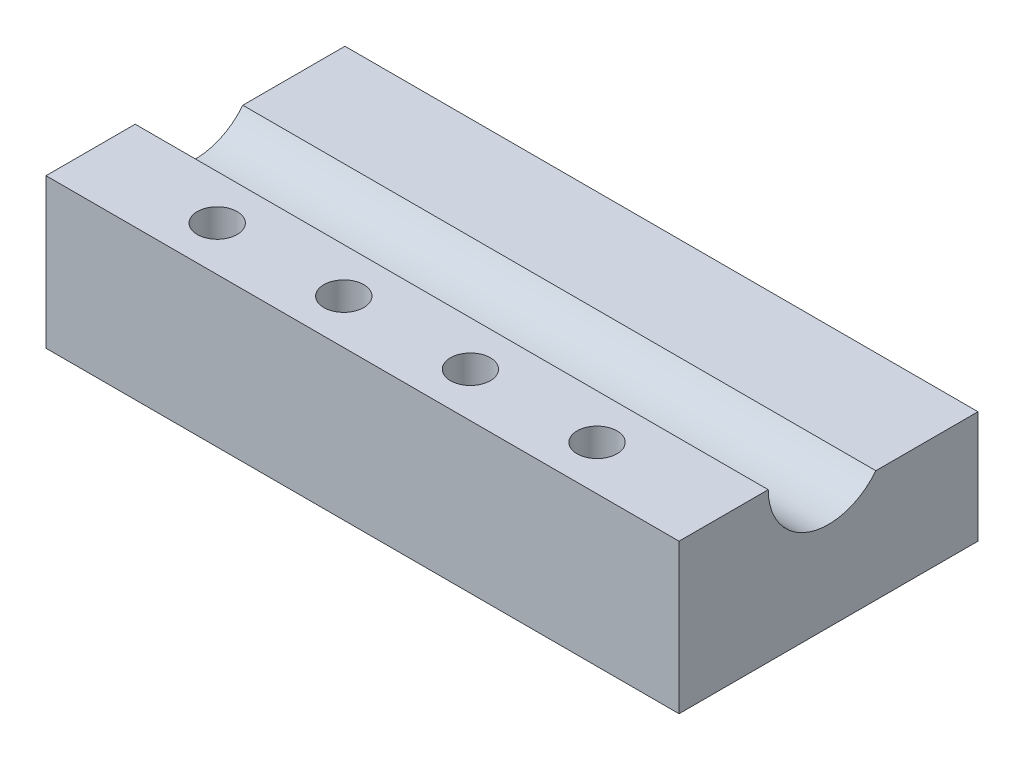
SolidWorks part; units mm, degrees
ref_plane "Front Plane" through (0, 0, 0) normal (0, 0, 1) x (1, 0, 0)
ref_plane "Top Plane" through (0, 0, 0) normal (0, 1, 0) x (1, 0, 0)
ref_plane "Right Plane" through (0, 0, 0) normal (1, 0, 0) x (0, 0, -1)
sketch "Sketch1" plane through (0, 0, 0) normal (0, 1, 0) x (1, 0, 0)
  line L1 (0, 0) -> (25.41, 0)
  line L2 (0, 0) -> (0, 12)
  line L3 (0, 12) -> (25.41, 12)
  line L4 (25.41, 0) -> (25.41, 12)
extrude "Boss-Extrude1" add sketch "Sketch1" along normal blind 6 contours L2 L3 L4 L1
sketch "Sketch2" plane through (0, 0, 0) normal (-1, 0, 0) x (0, 0, 1)
  line L0 (0, 6) -> (-12, 6) construction
  circle A0 centre (-6, 6) radius 2.42
extrude "Cut-Extrude1" cut sketch "Sketch2" against normal blind 25.41
sketch "Sketch3" plane through (0, 0, 0) normal (-1, 0, 0) x (0, 0, 1)
  line L1 (-12, 6) -> (-7.4565, 6)
  line L2 (-12, 6) -> (-12, 4.5)
  line L3 (-12, 4.5) -> (-7.4565, 4.5)
  line L4 (-7.4565, 6) -> (-7.4565, 4.5)
extrude "Cut-Extrude2" cut sketch "Sketch3" against normal blind 25.41
sketch "Sketch4" plane through (0, 6, 0) normal (0, 1, 0) x (1, 0, 0)
  line L0 (0, 1.79) -> (25.41, 1.79)
  line L1 (0, 0) -> (0, 3.58) construction
  line L2 (25.41, 0) -> (25.41, 3.58) construction
  line L3 (0, 1.79) -> (5.082, 1.79)
  line L4 (5.082, 1.79) -> (10.164, 1.79)
  line L5 (10.164, 1.79) -> (15.246, 1.79)
  line L6 (15.246, 1.79) -> (20.328, 1.79)
  circle A0 centre (5.082, 1.79) radius 0.8
  circle A1 centre (10.164, 1.79) radius 0.8
  circle A2 centre (15.246, 1.79) radius 0.8
  circle A3 centre (20.328, 1.79) radius 0.8
extrude "Cut-Extrude4" cut sketch "Sketch4" against normal through all contours A3 | A2 | A1 | A0
